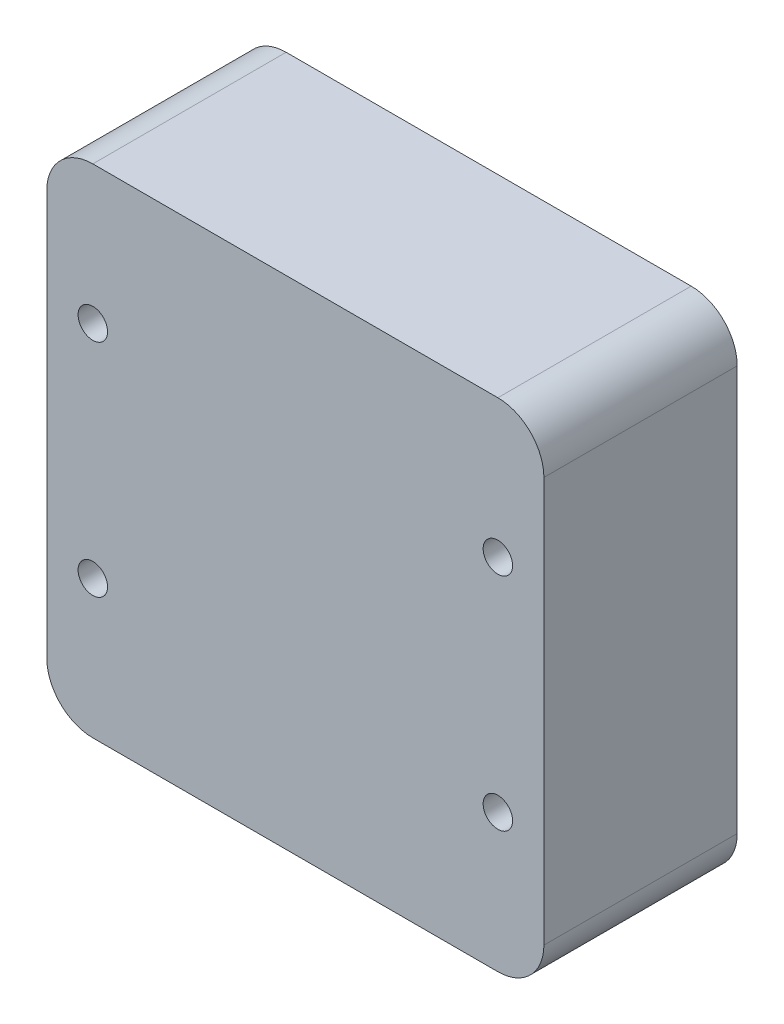
SolidWorks part; units mm, degrees
ref_plane "前视基准面" through (0, 0, 0) normal (0, 0, 1) x (1, 0, 0)
ref_plane "上视基准面" through (0, 0, 0) normal (0, 1, 0) x (1, 0, 0)
ref_plane "右视基准面" through (0, 0, 0) normal (1, 0, 0) x (0, 0, -1)
sketch "草图1" plane through (0, 0, 0) normal (0, 0, 1) x (1, 0, 0)
  line L1 (-24.4174, 16.0435) -> (29.5826, 16.0435)
  line L2 (-24.4174, 16.0435) -> (-24.4174, -37.9565)
  line L3 (-24.4174, -37.9565) -> (29.5826, -37.9565)
  line L4 (29.5826, 16.0435) -> (29.5826, -37.9565)
  dimension "D1" = 54
  dimension "D2" = 54
extrude "凸台-拉伸1" add sketch "草图1" along normal blind 21
fillet "圆角1" radius 5 4 edges at (-24.4174, 16.0435, 10.5) (-24.4174, -37.9565, 10.5) (29.5826, -37.9565, 10.5) (29.5826, 16.0435, 10.5)
sketch "草图2" plane through (0, 0, 21) normal (0, 0, 1) x (1, 0, 0)
  line L0 (-24.4174, 11.0435) -> (-24.4174, -32.9565) construction
  line L1 (-19.4174, 1.0435) -> (24.5826, 1.0435) construction
  line L2 (-19.4174, 1.0435) -> (-19.4174, -22.9565) construction
  line L3 (-19.4174, -22.9565) -> (24.5826, -22.9565) construction
  line L4 (24.5826, 1.0435) -> (24.5826, -22.9565) construction
  line L5 (-19.4174, -37.9565) -> (24.5826, -37.9565) construction
  circle A0 centre (24.5826, -22.9565) radius 1.6
  circle A1 centre (-19.4174, -22.9565) radius 1.6
  circle A2 centre (-19.4174, 1.0435) radius 1.6
  circle A3 centre (24.5826, 1.0435) radius 1.6
  point P6 (-24.4174, -10.9565)
  dimension "D1" = 44
  dimension "D2" = 24
  dimension "D3" = 5
  dimension "D4" = 15
extrude "切除-拉伸1" cut sketch "草图2" against normal blind 10
